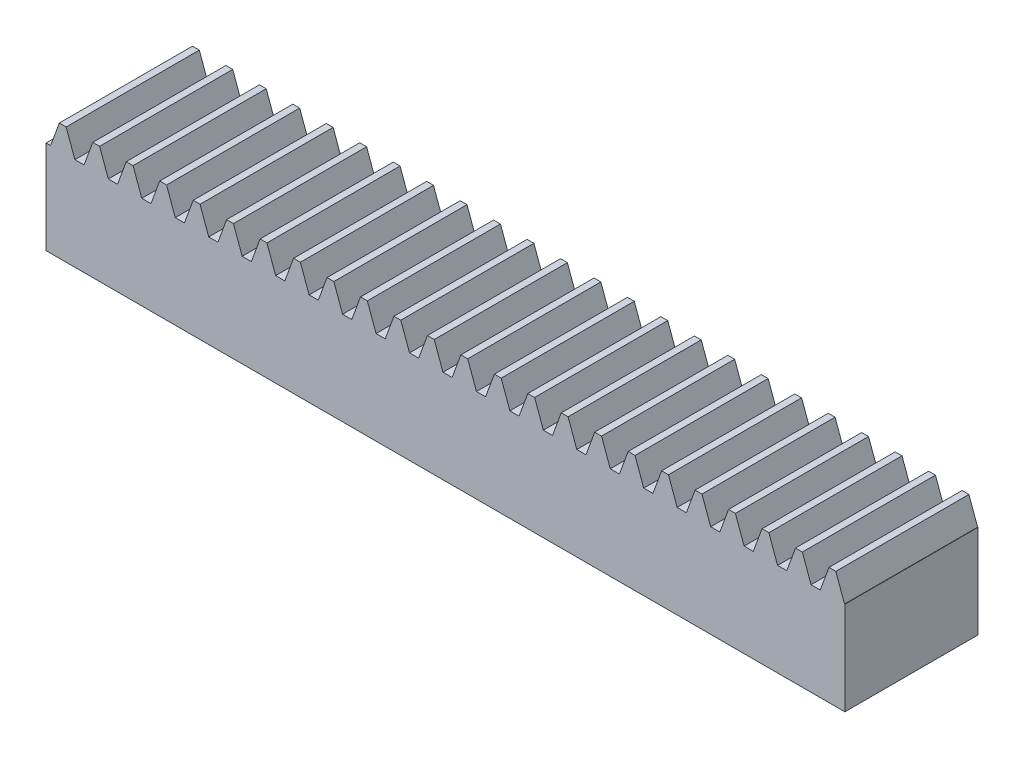
SolidWorks part; units mm, degrees
extrude "Blank" add sketch "BlankSke" against normal blind 25
sketch "BlankSke" plane through (0, 0, 0) normal (0, 0, 1) x (1, 0, 0)
  line L1 (0, 0) -> (150, 0)
  line L2 (0, 0) -> (0, 22)
  line L3 (0, 22) -> (150, 22)
  line L4 (150, 0) -> (150, 22)
  dimension "Length" = 150
  dimension "Blank_height" = 22
ref_plane "Plane1" through (0, 0, 0) normal (0, 0, 1) x (1, 0, 0)
ref_plane "Plane2" through (0, 0, 0) normal (0, 1, 0) x (1, 0, 0)
ref_plane "Plane3" through (0, 0, 0) normal (1, 0, 0) x (0, 0, -1)
sketch "HoldingSke" plane through (0, 0, 0) normal (0, 1, 0) x (1, 0, 0)
  line L0 (0, 0) -> (0.0696, 0.4951)
  line L1 (-15, 0) -> (100, 0) construction
  line L2 (0, 0) -> (-2.1039, 2.3779)
  line L3 (0, 0) -> (-11.863, 4.5341)
  line L4 (0, 0) -> (7.8269, 3.6497)
  line L5 (0, 0) -> (-23.7986, -8.8762)
  line L6 (0, 0) -> (-10.5278, -7.1032)
  line L9 (-71.009, 38.7566) -> (69.9449, 90.0596)
  line L10 (-76.2, 4.3779) -> (-56.2, 4.3779)
  line L11 (0, 0) -> (-25, 0)
  line L12 (-76.2, 101.6) -> (-76.133, 101.6)
  line L13 (24.9733, 27.94) -> (52.9518, 28.4284)
  line L14 (24.9733, 27.94) -> (24.9743, 27.94)
  line L15 (24.9733, 27.94) -> (100.4006, 29.5858)
  circle A0 centre (0, 0) radius 19.05
  circle A1 centre (0, 0) radius 10
  circle A2 centre (0, 0) radius 12.7
  dimension "MPH" = 20
  dimension "Diameter" = 38.1
  dimension "Num_teeth" = 25
  dimension "Pitch" = 0.5
  dimension "Show_teeth" = 998
  dimension "Thickness" = 12.7
  dimension "Ap" = 20
  dimension "Pitch_height" = 20
  dimension "Width" = 25
  dimension "Backlash" = 0.067
  dimension "Addendum_fac" = 1
  dimension "Dedendum_fac" = 1.25
  dimension "Clearance_fac" = 0.25
  dimension "Dedendum_add" = 0.001
  dimension "Length" = 150
  dimension "Module" = 2
sketch "TooCutSkeIll" plane through (0, 0, 0) normal (0, 0, 1) x (1, 0, 0)
  line L0 (-2.4806, 21.9474) -> (-0.9819, 17.8296)
  line L1 (-0.5111, 17.5) -> (0.5111, 17.5)
  line L2 (0.9819, 17.8296) -> (2.4806, 21.9474)
  line L3 (150, 22) -> (0, 22) construction
  line L4 (0, 0) -> (0, 64.897) construction
  line L5 (-13.208, 20) -> (12.954, 20) construction
  line L6 (0, 0) -> (150, 0) construction
  line L7 (1.7718, 20) -> (1.7718, 48.7463) construction
  line L8 (-1.7718, 20) -> (-1.7718, 48.7463) construction
  line L9 (2.5558, 22) -> (2.5558, 22.0254)
  line L10 (-2.5558, 22) -> (-2.5558, 22.0254)
  line L11 (-2.5558, 22.0254) -> (2.5558, 22.0254)
  arc A0 (0.5111, 17.5) -> (0.9819, 17.8296) centre (0.5111, 18.001) ccw
  arc A1 (-0.9819, 17.8296) -> (-0.5111, 17.5) centre (-0.5111, 18.001) ccw
  arc A2 (2.5558, 22) -> (2.4806, 21.9474) centre (2.5558, 21.92) ccw
  arc A3 (-2.4806, 21.9474) -> (-2.5558, 22) centre (-2.5558, 21.92) ccw
  dimension "Pitch_height" = 20
  dimension "Addendum_plus" = 2.0254
  dimension "Pressure_angle" = 20
  dimension "Gap_width" = 3.5436
  dimension "Dedendum" = 2.5
extrude "ToothCutIll" [suppressed] cut sketch "TooCutSkeIll" against normal through all
sketch "TooCutSkeSim" plane through (0, 0, 0) normal (0, 0, 1) x (1, 0, 0)
  line L0 (0.8619, 17.5) -> (-0.8619, 17.5)
  line L1 (2.509, 22.0254) -> (0.8619, 17.5)
  line L2 (0, 17.4625) -> (0, 53.467) construction
  line L3 (2.509, 22.0254) -> (-2.509, 22.0254)
  line L6 (-2.509, 22.0254) -> (-0.8619, 17.5)
  line L9 (-1.7718, 20) -> (1.7718, 20) construction
  line L10 (0, 0) -> (150, 0) construction
  line L11 (1.7718, 20) -> (1.7718, 53.467) construction
  line L12 (-1.7718, 20) -> (-1.7718, 53.467) construction
  dimension "Pitch_height" = 20
  dimension "Addendum_plus" = 2.0254
  dimension "Pressure_angle" = 20
  dimension "Gap_width" = 3.5436
  dimension "Dedendum" = 2.5
extrude "ToothCutSim" cut sketch "TooCutSkeSim" against normal through all
pattern_linear "TeethCuts" count 25 spacing 6.2832 along (1, 0, 0) of "ToothCutIll", "ToothCutSim"
equation "' \"Module@HoldingSke\" = 6.35"
equation "' \"Num_teeth@HoldingSke\" = 12"
equation "' \"Ap@HoldingSke\" =  20"
equation "' \"Ap@HoldingSke\" = 20"
equation "' \"Width@HoldingSke\" = 0.25 * 25.4"
equation "' \"Show_teeth@HoldingSke\" = 500"
equation "' \"Backlash@HoldingSke\" = 0.009 * 25.4"
equation "' \"Addendum_fac@HoldingSke\" = 1.0"
equation "' \"Dedendum_fac@HoldingSke\" = 1.25"
equation "' \"Dedendum_add@HoldingSke\" = 0.00005 * 25.4"
equation "' \"Clearance_fac@HoldingSke\" = 0.25"
equation "' \"Pitch_height@HoldingSke\" = 1 * 25.4"
equation "' \"Length@HoldingSke\" = 4.71 * 25.4"
equation "\"Pitch@HoldingSke\" = 1 / \"Module@HoldingSke\""
equation "\"MPH@HoldingSke\" = \"Dedendum_fac@HoldingSke\" / \"Pitch@HoldingSke\" + 2 * \"Dedendum_add@HoldingSke\" + 0.002 * 25.4"
equation "\"MPH@HoldingSke\" = ((sgn( \"MPH@HoldingSke\" - \"Pitch_height@HoldingSke\")+1)*( \"MPH@HoldingSke\" - \"Pitch_height@HoldingSke\"))/2 + \"Pitch_height@HoldingSke\""
equation "\"Blank_height@BlankSke\" = \"Pitch_height@HoldingSke\" + \"Addendum_fac@HoldingSke\"  / \"Pitch@HoldingSke\" "
equation "\"Length@BlankSke\" =  \"Length@HoldingSke\""
equation "\"Face_width@Blank\" = \"Width@HoldingSke\""
equation "\"Pressure_angle@TooCutSkeIll\" = \"Ap@HoldingSke\""
equation "\"Addendum_plus@TooCutSkeIll\" =  \"Addendum_fac@HoldingSke\"  / \"Pitch@HoldingSke\" + 0.001 *25.4"
equation "\"Dedendum@TooCutSkeIll\" = \"Dedendum_fac@HoldingSke\"  / \"Pitch@HoldingSke\""
equation "\"Pitch_height@TooCutSkeIll\" =  \"MPH@HoldingSke\""
equation "\"Gap_width@TooCutSkeIll\" = 3.14159265 / 2 / \"Pitch@HoldingSke\" + 6 * \"Backlash@HoldingSke\""
equation "\"Pressure_angle@TooCutSkeSim\" = \"Ap@HoldingSke\""
equation "\"Addendum_plus@TooCutSkeSim\" =  \"Addendum_fac@HoldingSke\"  / \"Pitch@HoldingSke\" + 0.001 * 25.4"
equation "\"Dedendum@TooCutSkeSim\" = \"Dedendum_fac@HoldingSke\"  / \"Pitch@HoldingSke\""
equation "\"Pitch_height@TooCutSkeSim\" =  \"MPH@HoldingSke\""
equation "\"Gap_width@TooCutSkeSim\" = 3.14159265 / 2 / \"Pitch@HoldingSke\" + 6 * \"Backlash@HoldingSke\""
equation "\"Root_fillet@TooCutSkeIll\" = \"Clearance_fac@HoldingSke\" / \"Pitch@HoldingSke\" + \"Dedendum_add@HoldingSke\""
equation "\"Break_rad@TooCutSkeIll\" = 0.02 / \"Pitch@HoldingSke\" * 2"
equation "\"Linear_pitch@TeethCuts\" = 3.14159265 / \"Pitch@HoldingSke\""
equation "\"Num_teeth@HoldingSke\" = int( ( \"Length@HoldingSke\" + 0 ) / (3.14159265 / \"Pitch@HoldingSke\")) + 0.9999  + 1"
equation " \"Num_teeth@TeethCuts\" = int( \"Show_teeth@HoldingSke\" ) + 1"
equation " \"Num_teeth@TeethCuts\" = ((sgn( \"Num_teeth@TeethCuts\" - \"Num_teeth@HoldingSke\" )-1)*( \"Num_teeth@TeethCuts\" - \"Num_teeth@HoldingSke\" ))/-2+ \"Num_teeth@HoldingSke\""
equation " \"Num_teeth@TeethCuts\" = ((sgn( \"Num_teeth@TeethCuts\" - 2.0)+1)*( \"Num_teeth@TeethCuts\" - 2.0))/2 +2.0"
